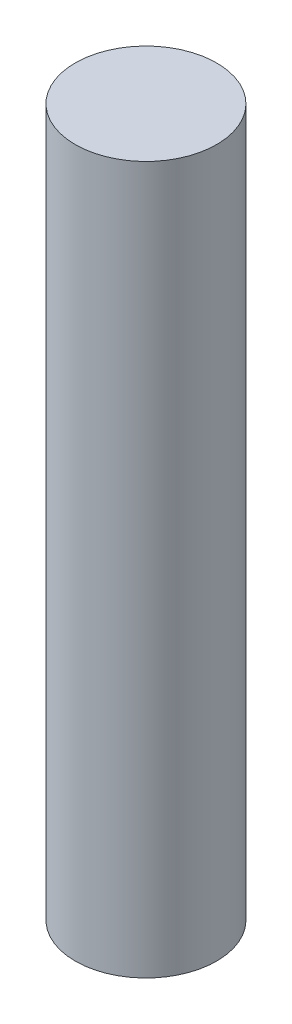
SolidWorks part; units mm, degrees
ref_plane "Front Plane" through (0, 0, 0) normal (0, 0, 1) x (1, 0, 0)
ref_plane "Top Plane" through (0, 0, 0) normal (0, 1, 0) x (1, 0, 0)
ref_plane "Right Plane" through (0, 0, 0) normal (1, 0, 0) x (0, 0, -1)
sketch "Sketch1" plane through (0, 0, 0) normal (0, 1, 0) x (1, 0, 0)
  circle A0 centre (0, 0) radius 5
  dimension "D1" = 10
extrude "Boss-Extrude1" add sketch "Sketch1" along normal blind 50
